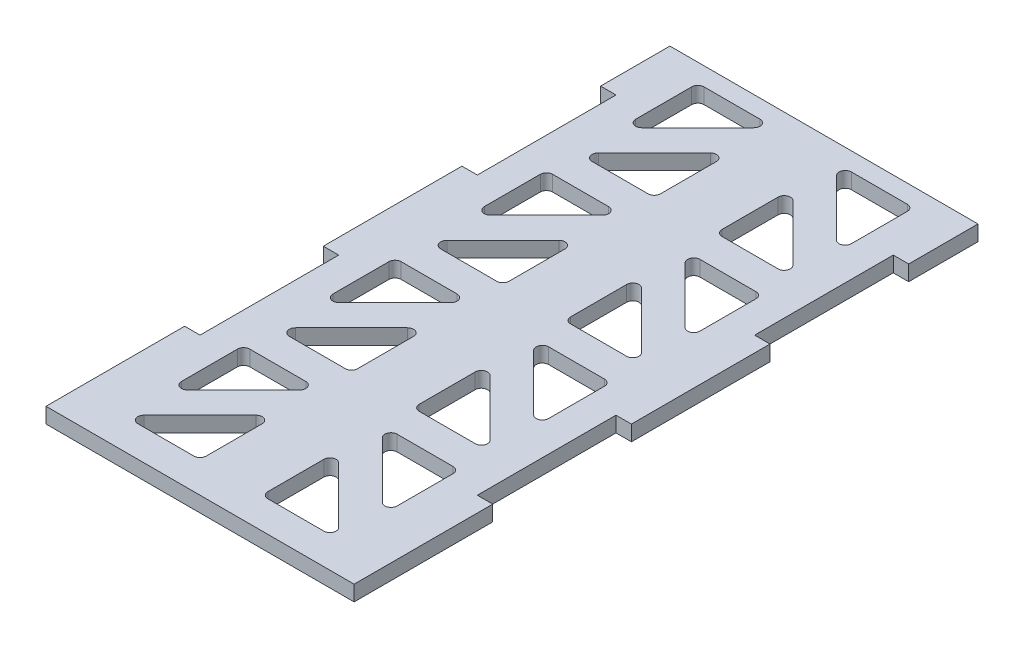
SolidWorks part; units mm, degrees
material "Balsa"
ref_plane "Front Plane" through (0, 0, 0) normal (0, 0, 1) x (1, 0, 0)
ref_plane "Top Plane" through (0, 0, 0) normal (0, 1, 0) x (1, 0, 0)
ref_plane "Right Plane" through (0, 0, 0) normal (1, 0, 0) x (0, 0, -1)
sketch "Sketch1" plane through (0, -9.7437, 0) normal (0, 1, 0) x (1, 0, 0)
  line L11 (28.575, 57.4509) -> (28.575, 28.8759)
  line L12 (28.575, 28.8759) -> (31.75, 28.8759)
  line L13 (31.75, 28.8759) -> (31.75, 0.3009)
  line L14 (31.75, 0.3009) -> (28.575, 0.3009)
  line L15 (28.575, 0.3009) -> (28.575, -28.2741)
  line L16 (28.575, -28.2741) -> (31.75, -28.2741)
  line L17 (31.75, -28.2741) -> (31.75, -56.8491)
  line L18 (31.75, -56.8491) -> (-31.75, -56.8491)
  line L19 (-31.75, -56.8491) -> (-31.75, -28.2741)
  line L20 (-31.75, -28.2741) -> (-28.575, -28.2741)
  line L21 (-28.575, -28.2741) -> (-28.575, 0.3009)
  line L22 (-28.575, 0.3009) -> (-31.75, 0.3009)
  line L23 (-31.75, 0.3009) -> (-31.75, 28.8759)
  line L24 (-31.75, 28.8759) -> (-28.575, 28.8759)
  line L25 (-28.575, 28.8759) -> (-28.575, 57.4509)
  line L137 (28.575, 57.4509) -> (31.75, 57.4509)
  line L143 (-31.75, 71.7384) -> (31.75, 71.7384)
  line L144 (-31.75, 71.7384) -> (-31.75, 57.4509)
  line L145 (-31.75, 57.4509) -> (-28.575, 57.4509)
  line L146 (31.75, 71.7384) -> (31.75, 57.4509)
  dimension "D3" = 14.2875
extrude "Boss-Extrude1" add sketch "Sketch1" along normal blind 3.175
sketch "Sketch2" plane through (0, -6.5687, 0) normal (0, 1, 0) x (1, 0, 0)
  line L0 (-22.225, -50.4991) -> (-6.35, -50.4991)
  line L1 (-6.35, -50.4991) -> (-6.35, -34.6241)
  line L2 (-6.35, -34.6241) -> (-22.225, -50.4991)
  line L3 (-28.575, 0.3009) -> (-28.575, -28.2741) construction
  line L4 (0, -56.8491) -> (0, 71.7384) construction
  line L5 (-31.75, -56.8491) -> (31.75, -56.8491) construction
  line L6 (31.75, 71.7384) -> (-31.75, 71.7384) construction
  line L7 (-22.225, -41.5189) -> (-6.35, -25.6439)
  line L8 (-6.35, -25.6439) -> (-22.225, -25.6439)
  line L9 (-22.225, -25.6439) -> (-22.225, -41.5189)
  line L10 (-6.35, -3.4189) -> (-22.225, -19.2939)
  line L11 (-22.225, -19.2939) -> (-6.35, -19.2939)
  line L12 (-6.35, -19.2939) -> (-6.35, -3.4189)
  line L13 (-22.225, 5.5614) -> (-22.225, -10.3136)
  line L14 (-22.225, -10.3136) -> (-6.35, 5.5614)
  line L15 (-6.35, 5.5614) -> (-22.225, 5.5614)
  line L16 (-6.35, 27.7864) -> (-22.225, 11.9114)
  line L17 (-22.225, 11.9114) -> (-6.35, 11.9114)
  line L18 (-6.35, 11.9114) -> (-6.35, 27.7864)
  line L19 (-22.225, 36.7666) -> (-22.225, 20.8916)
  line L20 (-22.225, 20.8916) -> (-6.35, 36.7666)
  line L21 (-6.35, 36.7666) -> (-22.225, 36.7666)
  line L22 (-6.35, 58.9916) -> (-22.225, 43.1166)
  line L23 (-22.225, 43.1166) -> (-6.35, 43.1166)
  line L24 (-6.35, 43.1166) -> (-6.35, 58.9916)
  line L25 (-22.225, 67.9719) -> (-22.225, 52.0969)
  line L26 (-22.225, 52.0969) -> (-6.35, 67.9719)
  line L27 (-6.35, 67.9719) -> (-22.225, 67.9719)
  dimension "D1" = 6.35
  dimension "D2" = 6.35
  dimension "D3" = 6.35
  dimension "D5" = 6.35
  dimension "D4" = 15.875
  dimension "D7" = 6.35
  dimension "D6" = 4
extrude "Cut-Extrude1" cut sketch "Sketch2" against normal through all
fillet "Fillet1" radius 1.27 24 edges at (-22.225, -8.1562, 50.4991) (-6.35, -8.1562, 50.4991) (-22.225, -8.1562, 41.5189) (-6.35, -8.1562, 34.6241) (-6.35, -8.1562, 25.6439) (-22.225, -8.1562, 25.6439) (-6.35, -8.1562, -67.9719) (-6.35, -8.1562, -36.7666) (-6.35, -8.1562, -43.1166) (-6.35, -8.1562, -11.9114) (-6.35, -8.1562, 19.2939) (-22.225, -8.1562, 19.2939) (-22.225, -8.1562, -11.9114) (-22.225, -8.1562, -43.1166) (-22.225, -8.1562, -5.5614) (-22.225, -8.1562, -36.7666) (-22.225, -8.1562, -67.9719) (-22.225, -8.1562, 10.3136) (-22.225, -8.1562, -20.8916) (-22.225, -8.1562, -52.0969) (-6.35, -8.1562, -58.9916) (-6.35, -8.1562, -27.7864) (-6.35, -8.1562, -5.5614) (-6.35, -8.1562, 3.4189)
mirror "Mirror1" about plane through (0, 0, 0) normal (1, 0, 0) of "Cut-Extrude1", "Fillet1"
equation "\"Spacing\"= 0.25"
equation "\"D1@Sketch2\"=\"Spacing\""
equation "\"D2@Sketch2\"=\"Spacing\""
equation "\"D3@Sketch2\"=\"Spacing\""
equation "\"D5@Sketch2\"=\"Spacing\""
equation "\"D7@Sketch2\"=\"Spacing\""
